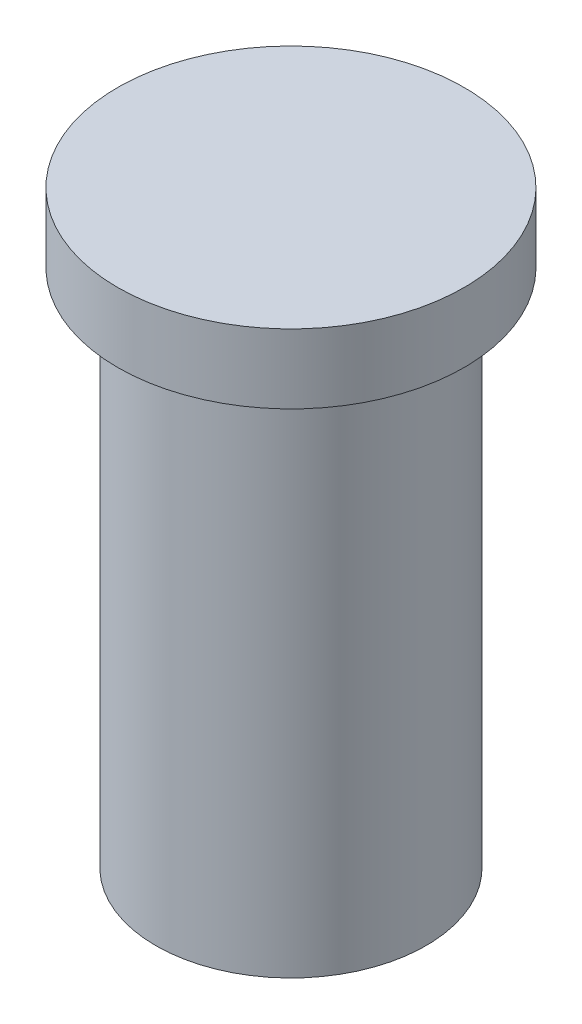
SolidWorks part; units mm, degrees
ref_plane "Front Plane" through (0, 0, 0) normal (0, 0, 1) x (1, 0, 0)
ref_plane "Top Plane" through (0, 0, 0) normal (0, 1, 0) x (1, 0, 0)
ref_plane "Right Plane" through (0, 0, 0) normal (1, 0, 0) x (0, 0, -1)
sketch "Sketch1" plane through (0, 0, 0) normal (0, 1, 0) x (1, 0, 0)
  circle A0 centre (0, 0) radius 3.9
  dimension "D2" = 7.8
extrude "Boss-Extrude1" add sketch "Sketch1" along normal blind 15
sketch "Sketch2" plane through (0, 15, 0) normal (0, 1, 0) x (1, 0, 0)
  circle A2 centre (0, 0) radius 5
  dimension "D1" = 10
extrude "Boss-Extrude2" add sketch "Sketch2" along normal blind 2
